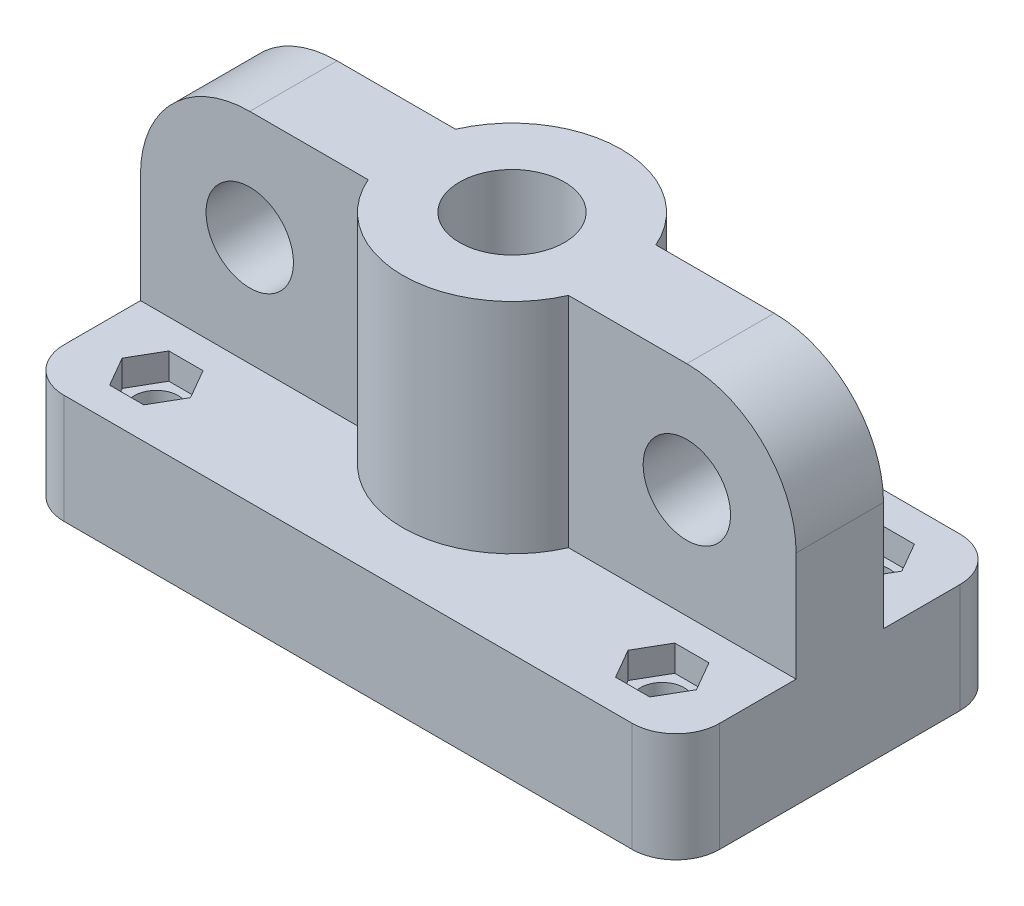
SolidWorks part; units mm, degrees
ref_plane "Front Plane" through (0, 0, 0) normal (0, 0, 1) x (1, 0, 0)
ref_plane "Top Plane" through (0, 0, 0) normal (0, 1, 0) x (1, 0, 0)
ref_plane "Right Plane" through (0, 0, 0) normal (1, 0, 0) x (0, 0, -1)
sketch "Sketch2" plane through (0, 0, 0) normal (0, 1, 0) x (1, 0, 0)
  line L1 (-30, 15) -> (30, 15)
  line L2 (-30, 15) -> (-30, -15)
  line L3 (-30, -15) -> (30, -15)
  line L4 (30, 15) -> (30, -15)
  point P4 (0, 15)
  point P6 (-30, 0)
  dimension "D1" = 60
  dimension "D2" = 30
extrude "Base" add sketch "Sketch2" along normal blind 10
sketch "Sketch3" plane through (0, 10, 0) normal (0, 1, 0) x (1, 0, 0)
  line L1 (-30, 4) -> (30, 4)
  line L2 (-30, 4) -> (-30, -4)
  line L3 (-30, -4) -> (30, -4)
  line L4 (30, 4) -> (30, -4)
  circle A0 centre (0, 0) radius 10
  point P7 (-30, 0)
  point P8 (0, 4)
  line M1 (-30, 15) -> (-30, -15)
  line M3 (30, -15) -> (30, 15)
  dimension "D1" = 20
  dimension "D2" = 8
  dimension "D3" = 60
extrude "Structure" add sketch "Sketch3" along normal blind 20 contours A0 L1 L3 M1 | L1 A0 | L3 A0 L1 | L3 A0 | A0 L3 L1 M3
sketch "Sketch4" plane through (0, 0, 4) normal (0, 0, 1) x (1, 0, 0)
  line L0 (-30, 30) -> (-30, 10) construction
  line L1 (-30, 30) -> (-9.1652, 30) construction
  line L2 (-9.1652, 30) -> (9.1652, 30) construction
  line L3 (0, 30) -> (0, 0) construction
  circle A0 centre (-20, 20) radius 4
  circle A1 centre (20, 20) radius 4
  dimension "D3" = 8
  dimension "D1" = 10
  dimension "D2" = 10
extrude "Elastic Holes" cut sketch "Sketch4" against normal through all
sketch "Sketch5" plane through (0, 30, 0) normal (0, 1, 0) x (1, 0, 0)
  circle A0 centre (0, 0) radius 4.8
  dimension "D1" = 9.6
extrude "Pen Hole" cut sketch "Sketch5" against normal through all
fillet "Upper Corner Dec" radius 10 2 edges at (30, 30, 0) (-30, 30, 0)
fillet "Base Corner Dec" radius 4 4 edges at (-30, 5, -15) (30, 5, -15) (30, 5, 15) (-30, 5, 15)
sketch "Sketch6" plane through (0, 0, 0) normal (0, -1, 0) x (1, 0, 0)
  line L0 (0, 20.5685) -> (0, -23.7301) construction
  line L1 (-40.8173, 0) -> (41.4271, 0) construction
  circle A0 centre (-23.15, 9.4) radius 2
  circle A1 centre (23.15, 9.4) radius 2
  circle A2 centre (23.15, -9.4) radius 2
  circle A3 centre (-23.15, -9.4) radius 2
  dimension "D1" = 4
  dimension "D2" = 23.15
  dimension "D3" = 9.4
extrude "Bolt Holes" cut sketch "Sketch6" against normal through all
sketch "Sketch7" plane through (0, 10, 0) normal (0, 1, 0) x (1, 0, 0)
  line L1 (-21.5854, 12.11) -> (-24.7146, 12.11)
  line L2 (-24.7146, 12.11) -> (-26.2792, 9.4)
  line L3 (-26.2792, 9.4) -> (-24.7146, 6.69)
  line L4 (-24.7146, 6.69) -> (-21.5854, 6.69)
  line L5 (-21.5854, 6.69) -> (-20.0208, 9.4)
  line L6 (-20.0208, 9.4) -> (-21.5854, 12.11)
  line L8 (26, 15) -> (-26, 15) construction
  line L9 (0, 18.7668) -> (0, -21.6147) construction
  line L10 (-35.0509, 0) -> (35.489, 0) construction
  line L13 (20.0208, 9.4) -> (21.5854, 12.11)
  line L14 (21.5854, 6.69) -> (20.0208, 9.4)
  line L15 (24.7146, 6.69) -> (21.5854, 6.69)
  line L16 (26.2792, 9.4) -> (24.7146, 6.69)
  line L17 (24.7146, 12.11) -> (26.2792, 9.4)
  line L18 (21.5854, 12.11) -> (24.7146, 12.11)
  line L19 (21.5854, -12.11) -> (24.7146, -12.11)
  line L20 (24.7146, -12.11) -> (26.2792, -9.4)
  line L21 (26.2792, -9.4) -> (24.7146, -6.69)
  line L22 (24.7146, -6.69) -> (21.5854, -6.69)
  line L23 (21.5854, -6.69) -> (20.0208, -9.4)
  line L24 (20.0208, -9.4) -> (21.5854, -12.11)
  line L25 (-20.0208, -9.4) -> (-21.5854, -12.11)
  line L26 (-21.5854, -6.69) -> (-20.0208, -9.4)
  line L27 (-24.7146, -6.69) -> (-21.5854, -6.69)
  line L28 (-26.2792, -9.4) -> (-24.7146, -6.69)
  line L29 (-24.7146, -12.11) -> (-26.2792, -9.4)
  line L30 (-21.5854, -12.11) -> (-24.7146, -12.11)
  circle A0 centre (-23.15, 9.4) radius 2.71 construction
  circle A1 centre (23.15, 9.4) radius 2.71 construction
  circle A2 centre (23.15, -9.4) radius 2.71 construction
  circle A3 centre (-23.15, -9.4) radius 2.71 construction
  dimension "D1" = 5.42
extrude "Cap Nut Holes" cut sketch "Sketch7" against normal blind 2.4
